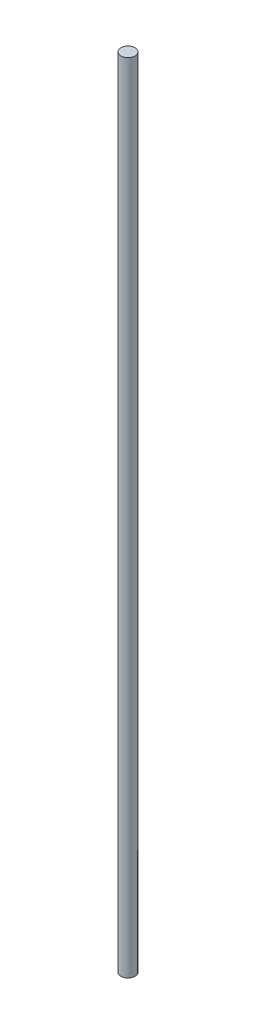
SolidWorks part; units mm, degrees
ref_plane "Front Plane" through (0, 0, 0) normal (0, 0, 1) x (1, 0, 0)
ref_plane "Top Plane" through (0, 0, 0) normal (0, 1, 0) x (1, 0, 0)
ref_plane "Right Plane" through (0, 0, 0) normal (1, 0, 0) x (0, 0, -1)
sketch "Sketch1" plane through (0, 0, 0) normal (0, 1, 0) x (1, 0, 0)
  circle A0 centre (0, 0) radius 1.5875
  dimension "D1" = 3.175
extrude "Boss-Extrude1" add sketch "Sketch1" along normal blind 177.8
